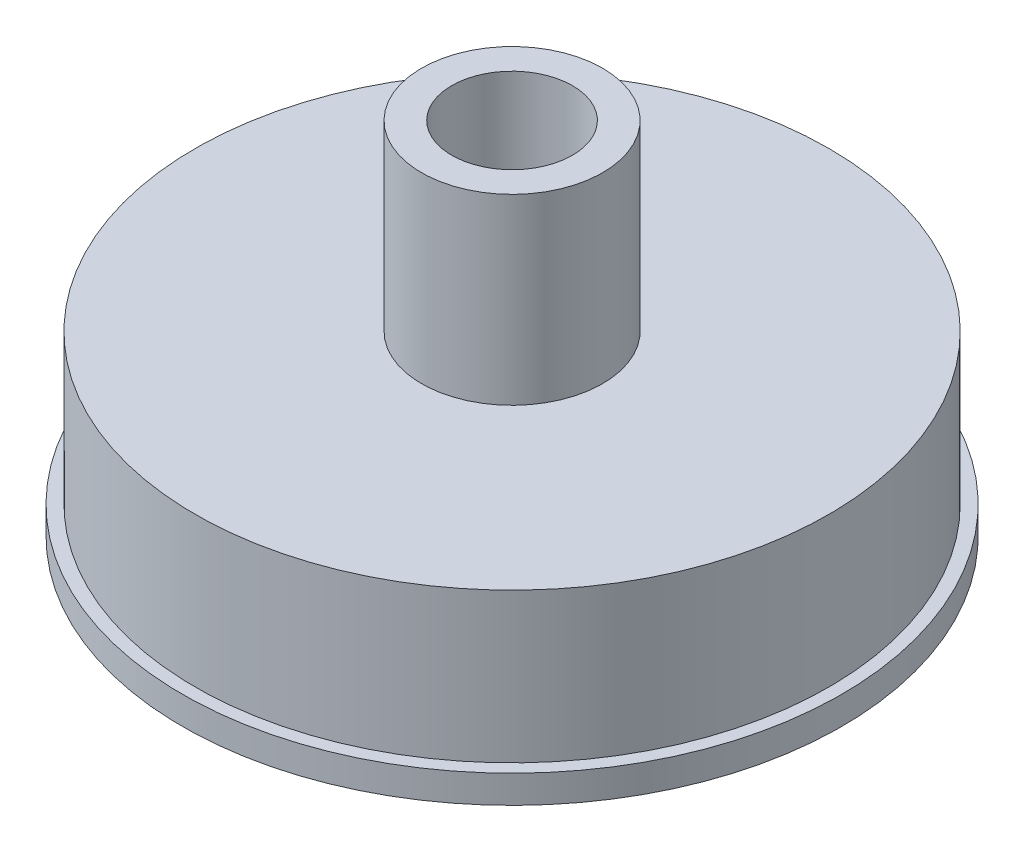
SolidWorks part; units mm, degrees
material "6061-T6 (SS)"
ref_plane "Front Plane" through (0, 0, 0) normal (0, 0, 1) x (1, 0, 0)
ref_plane "Top Plane" through (0, 0, 0) normal (0, 1, 0) x (1, 0, 0)
ref_plane "Right Plane" through (0, 0, 0) normal (1, 0, 0) x (0, 0, -1)
sketch "Sketch1" plane through (0, 0, 0) normal (0, 0, 1) x (1, 0, 0)
  line L0 (0, 0) -> (0, 48.4635) construction
  line L1 (26, 2.2) -> (25, 2.2)
  line L2 (21, 0) -> (26, 0)
  line L3 (21, 0) -> (21, 11)
  line L4 (25, 2.2) -> (25, 14)
  line L5 (26, 0) -> (26, 2.2)
  line L6 (25, 14) -> (7.1438, 14)
  line L7 (21, 11) -> (4.7625, 11)
  line L8 (4.7625, 11) -> (4.7625, 28.4125)
  line L11 (7.1438, 14) -> (7.1437, 28.4125)
  line L12 (7.1437, 28.4125) -> (4.7625, 28.4125)
  dimension "D1" = 52
  dimension "D2" = 42
  dimension "D3" = 11
  dimension "D4" = 50
  dimension "D5" = 3
  dimension "D6" = 11.8
  dimension "D7" = 9.525
  dimension "D10" = 14.2875
  dimension "D11" = 14.4125
revolve "Revolve1" add sketch "Sketch1" angle 360 about L0
